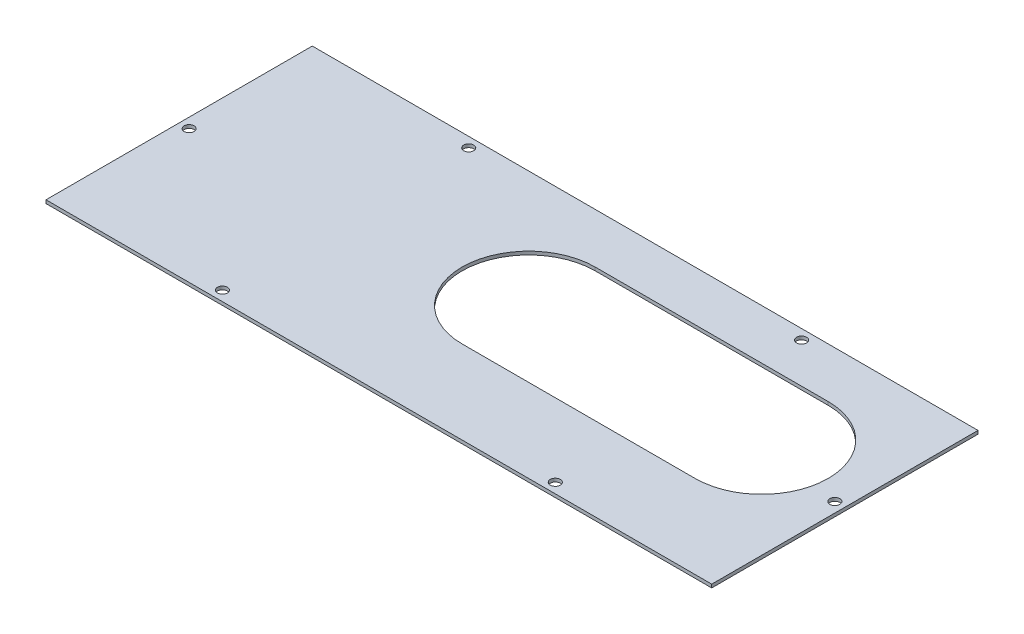
SolidWorks part; units mm, degrees
material "普通碳钢"
ref_plane "前视基准面" through (0, 0, 0) normal (0, 0, 1) x (1, 0, 0)
ref_plane "上视基准面" through (0, 0, 0) normal (0, 1, 0) x (1, 0, 0)
ref_plane "右视基准面" through (0, 0, 0) normal (1, 0, 0) x (0, 0, -1)
sketch "草图1" plane through (0, 0, 0) normal (0, 1, 0) x (1, 0, 0)
  line L1 (-100, 40) -> (100, 40)
  line L2 (-100, 40) -> (-100, -40)
  line L3 (-100, -40) -> (100, -40)
  line L4 (100, 40) -> (100, -40)
  dimension "D1" = 200
  dimension "D2" = 80
  dimension "D3" = 40
  dimension "D4" = 100
extrude "凸台-拉伸1" add sketch "草图1" along normal blind 1
sketch "草图2" plane through (0, 1, 0) normal (0, 1, 0) x (1, 0, 0)
  line L0 (0, 5) -> (70, 5) construction
  line L1 (0, 25) -> (70, 25)
  line L2 (0, -15) -> (70, -15)
  line L4 (100, -40) -> (100, 40) construction
  line L5 (100, 40) -> (-100, 40) construction
  arc A0 (0, 25) -> (0, -15) centre (0, 5) ccw
  arc A1 (70, -15) -> (70, 25) centre (70, 5) ccw
  point P2 (35, 5)
  dimension "D1" = 15
  dimension "D2" = 40
  dimension "D3" = 30
  dimension "D4" = 70
extrude "切除-拉伸1" cut sketch "草图2" against normal up to next
sketch "草图3" plane through (0, 1, 0) normal (0, 1, 0) x (1, 0, 0)
  line L2 (-100, 40) -> (-100, -40) construction
  line L3 (100, 40) -> (-100, 40) construction
  line L4 (-100, -40) -> (100, -40) construction
  line L5 (100, -40) -> (100, 40) construction
  circle A0 centre (-50, 37) radius 1.5
  circle A1 centre (50, 37) radius 1.5
  circle A2 centre (50, -37) radius 1.5
  circle A3 centre (-50, -37) radius 1.5
  circle A4 centre (-97, 0) radius 1.5
  circle A5 centre (97, 0) radius 1.5
  dimension "D1" = 3
  dimension "D2" = 3
  dimension "D3" = 3
  dimension "D4" = 3
  dimension "D5" = 3
  dimension "D6" = 3
  dimension "D7" = 100
  dimension "D9" = 100
  dimension "D11" = 40
  dimension "D12" = 40
  dimension "D14" = 3
  dimension "D15" = 3
  dimension "D16" = 3
  dimension "D17" = 3
  dimension "D18" = 3
  dimension "D8" = 50
  dimension "D10" = 50
  dimension "D13" = 3
extrude "切除-拉伸2" cut sketch "草图3" against normal blind 10
